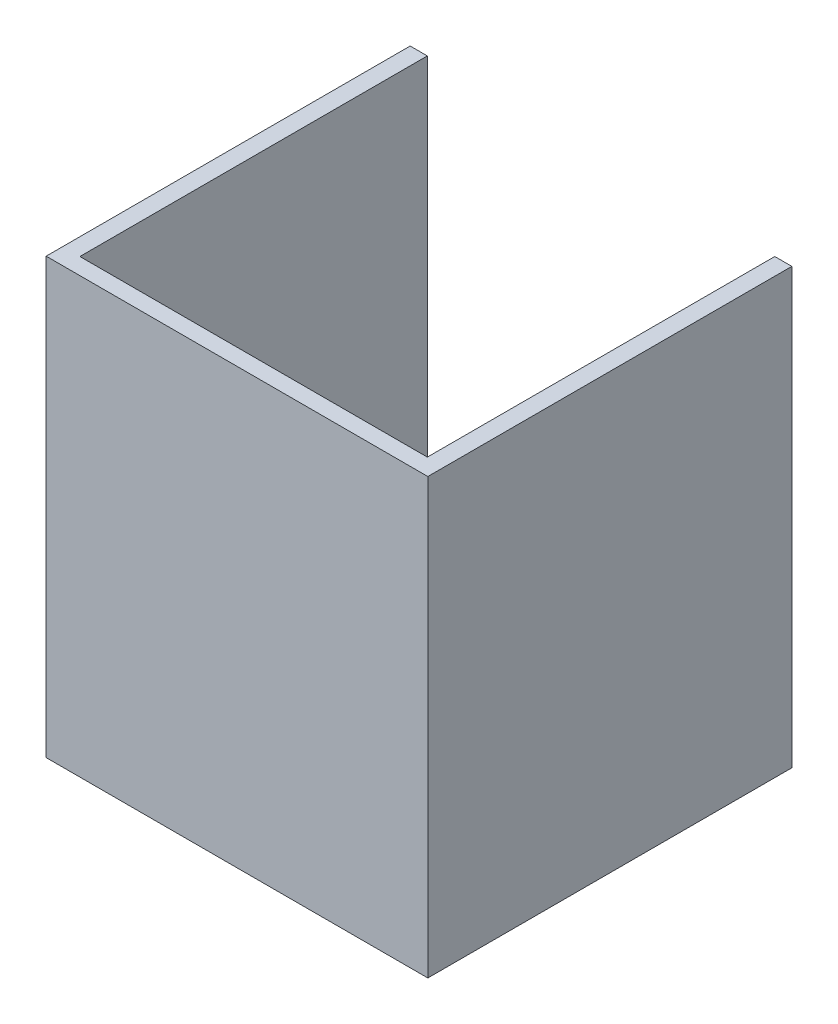
SolidWorks part; units mm, degrees
ref_plane "Alzado" through (0, 0, 0) normal (0, 0, 1) x (1, 0, 0)
ref_plane "Planta" through (0, 0, 0) normal (0, 1, 0) x (1, 0, 0)
ref_plane "Vista lateral" through (0, 0, 0) normal (1, 0, 0) x (0, 0, -1)
sketch "Croquis1" plane through (0, 0, 0) normal (0, 1, 0) x (1, 0, 0)
  line L0 (0, 0) -> (0, -50.8)
  line L1 (0, -50.8) -> (-50.8, -50.8)
  line L2 (-50.8, -50.8) -> (-50.8, 0)
  line L3 (0, 0) -> (2.4934, 0)
  line L4 (2.4934, 0) -> (2.4934, -53.222)
  line L5 (2.4934, -53.222) -> (-53.31, -53.222)
  line L6 (-53.31, -53.222) -> (-53.31, 0)
  line L7 (-53.31, 0) -> (-50.8, 0)
  dimension "D1" = 50.8
  dimension "D2" = 50.8
extrude "Saliente-Extruir1" add sketch "Croquis1" along normal blind 63.5 contours L1 L2 L7 L6 L5 L4 L3 L0
